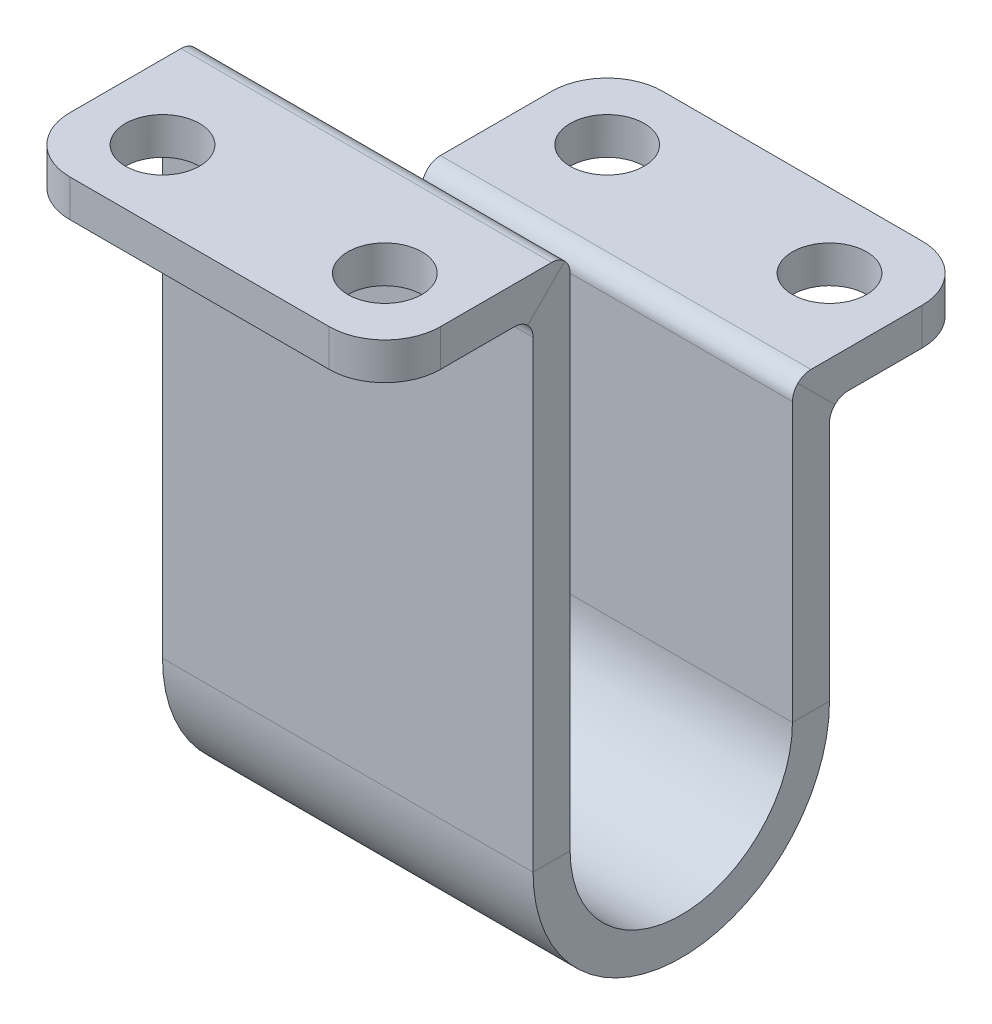
SolidWorks part; units mm, degrees
ref_plane "Front Plane" through (0, 0, 0) normal (0, 0, 1) x (1, 0, 0)
ref_plane "Top Plane" through (0, 0, 0) normal (0, 1, 0) x (1, 0, 0)
ref_plane "Right Plane" through (0, 0, 0) normal (1, 0, 0) x (0, 0, -1)
sketch "Sketch1" plane through (0, 0, 0) normal (1, 0, 0) x (0, 0, -1)
  line L0 (0, 0) -> (22.5, 0)
  line L1 (22.5, 0) -> (22.5, -67.5)
  line L2 (57.5, -67.5) -> (57.5, -30)
  line L3 (57.5, -30) -> (80, -30)
  arc A0 (22.5, -67.5) -> (57.5, -67.5) centre (40, -67.5) ccw
  dimension "D3" = 17.5
  dimension "D1" = 22.5
  dimension "D2" = 67.5
  dimension "D4" = 37.5
  dimension "D5" = 22.5
sketch "Sketch2" plane through (0, 0, 0) normal (0, 0, 1) x (1, 0, 0)
  line L1 (-25, 2.5) -> (25, 2.5)
  line L2 (-25, 2.5) -> (-25, -2.5)
  line L3 (-25, -2.5) -> (25, -2.5)
  line L4 (25, 2.5) -> (25, -2.5)
  line L5 (-25, 2.5) -> (25, -2.5) construction
  line L6 (-25, -2.5) -> (25, 2.5) construction
  point P0 (0, 0)
  dimension "D1" = 50
  dimension "D2" = 5
sweep "Sweep1" add profiles "Sketch2" path "Sketch1"
fillet "Fillet2" radius 2.5 4 edges at (0, -32.5, -60) (0, -27.5, -55) (0, 2.5, -25) (0, -2.5, -20)
sketch "Sketch3" plane through (0, 2.5, 0) normal (0, 1, 0) x (1, 0, 0)
  line L0 (25, 80) -> (-25, 80) construction
  line L1 (0, 80) -> (0, 0) construction
  line L3 (0, 70) -> (-25, 70) construction
  line L4 (-25, 57.5) -> (-25, 80) construction
  line L5 (25, 55) -> (-25, 55) construction
  line L6 (-25, 40) -> (25, 40) construction
  line L7 (-25, 55) -> (-25, 25) construction
  line L8 (25, 25) -> (25, 55) construction
  circle A0 centre (-15, 70) radius 5
  circle A2 centre (15, 70) radius 5
  circle A3 centre (15, 10) radius 5
  circle A4 centre (-15, 10) radius 5
  dimension "D1" = 10
  dimension "D2" = 15
  dimension "D3" = 15
extrude "Cut-Extrude1" cut sketch "Sketch3" against normal blind 50
fillet "Fillet3" radius 7.5 4 edges at (25, 0, 0) (-25, 0, 0) (25, -30, -80) (-25, -30, -80)
